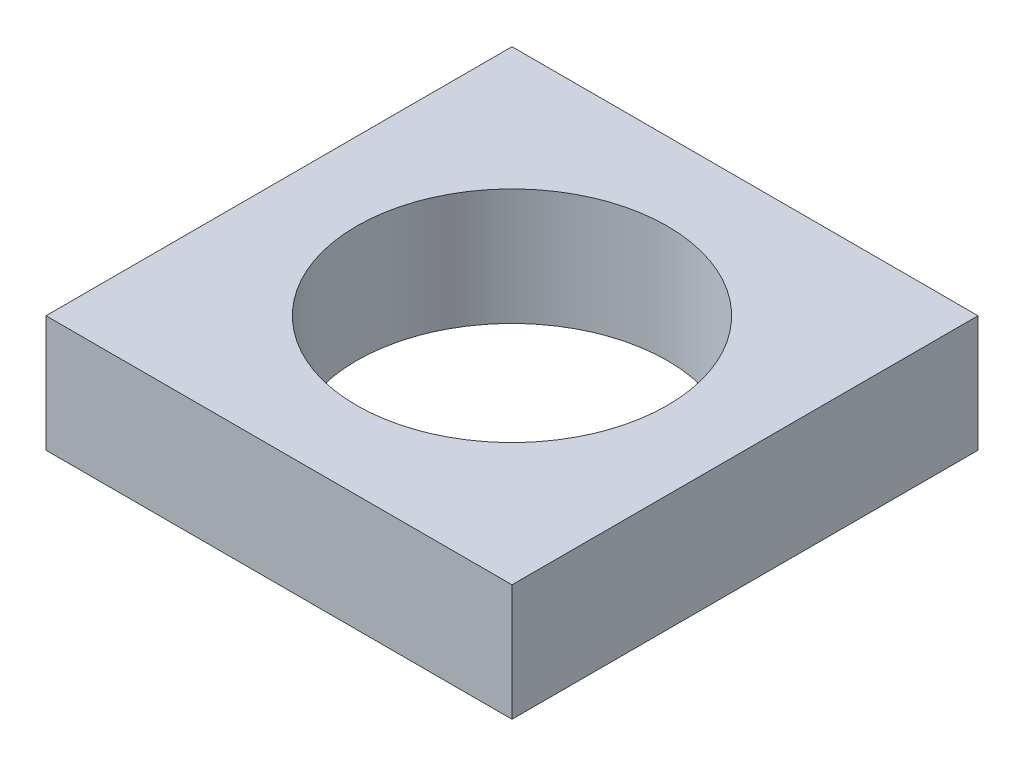
SolidWorks part; units mm, degrees
ref_plane "Front Plane" through (0, 0, 0) normal (0, 0, 1) x (1, 0, 0)
ref_plane "Top Plane" through (0, 0, 0) normal (0, 1, 0) x (1, 0, 0)
ref_plane "Right Plane" through (0, 0, 0) normal (1, 0, 0) x (0, 0, -1)
sketch "Sketch1" plane through (0, 0, 0) normal (0, 1, 0) x (1, 0, 0)
  line L5 (-6, 6) -> (6, 6)
  line L6 (-6, 6) -> (-6, -6)
  line L7 (-6, -6) -> (6, -6)
  line L8 (6, 6) -> (6, -6)
  line L9 (-6, 6) -> (6, -6) construction
  line L10 (-6, -6) -> (6, 6) construction
  circle A0 centre (0, 0) radius 4
  dimension "D1" = 8
  dimension "D2" = 12
extrude "Boss-Extrude2" add sketch "Sketch1" along normal blind 3
